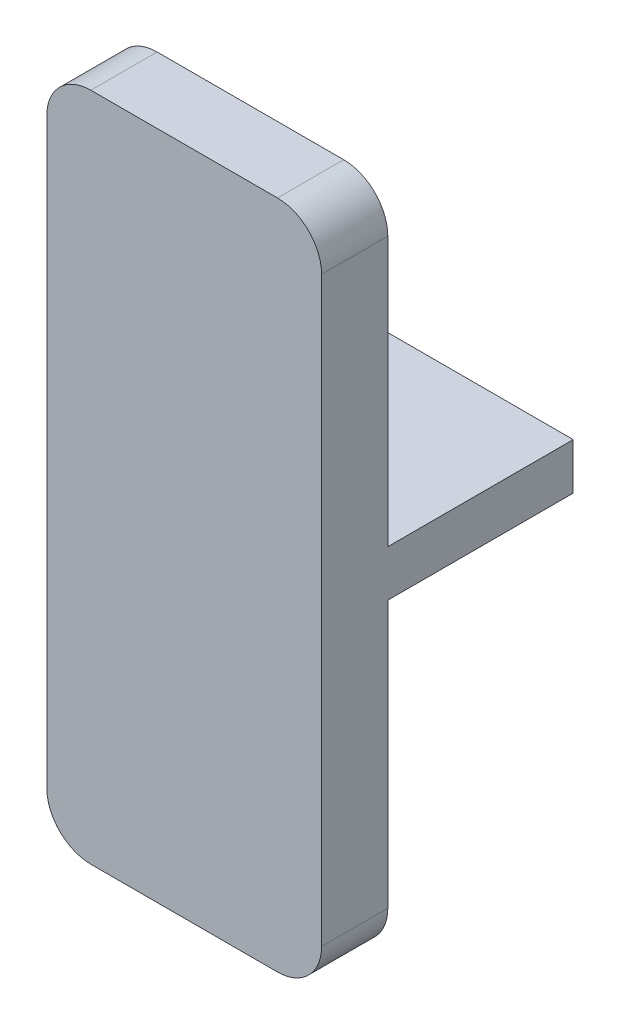
SolidWorks part; units mm, degrees
ref_plane "Plan de face" through (0, 0, 0) normal (0, 0, 1) x (1, 0, 0)
ref_plane "Plan de dessus" through (0, 0, 0) normal (0, 1, 0) x (1, 0, 0)
ref_plane "Plan de droite" through (0, 0, 0) normal (1, 0, 0) x (0, 0, -1)
sketch "Esquisse1" plane through (0, 0, 0) normal (0, 0, 1) x (1, 0, 0)
  line L0 (12.45, 0) -> (0, 2.1) construction
  line L1 (0, 0) -> (12.45, 0)
  line L2 (0, 0) -> (0, 2.1)
  line L3 (0, 2.1) -> (12.45, 2.1)
  line L4 (12.45, 0) -> (12.45, 2.1)
  line L5 (0, 0) -> (12.45, 2.1) construction
  dimension "D1" = 12.45
  dimension "D2" = 2.1
extrude "Boss.-Extru.1" add sketch "Esquisse1" along normal blind 8.4
sketch "Esquisse2" plane through (0, 0, 8.4) normal (0, 0, 1) x (1, 0, 0)
  line L0 (12.45, 2.1) -> (0, 2.1) construction
  line L5 (0, 16.2817) -> (12.45, 16.2817)
  line L6 (0, 16.2817) -> (0, -14.0864)
  line L7 (0, -14.0864) -> (12.45, -14.0864)
  line L8 (12.45, 16.2817) -> (12.45, -14.0864)
  line L9 (0, 16.2817) -> (12.45, -14.0864) construction
  line L10 (0, -14.0864) -> (12.45, 16.2817) construction
  line L11 (12.45, 0) -> (12.45, 2.1) construction
  point P0 (-7.5604, 16.2817)
  point P1 (6.225, 1.0977)
extrude "Boss.-Extru.2" add sketch "Esquisse2" along normal blind 3
fillet "Congé1" radius 2 4 edges at (12.45, -14.0864, 9.9) (0, -14.0864, 9.9) (12.45, 16.2817, 9.9) (0, 16.2817, 9.9)
